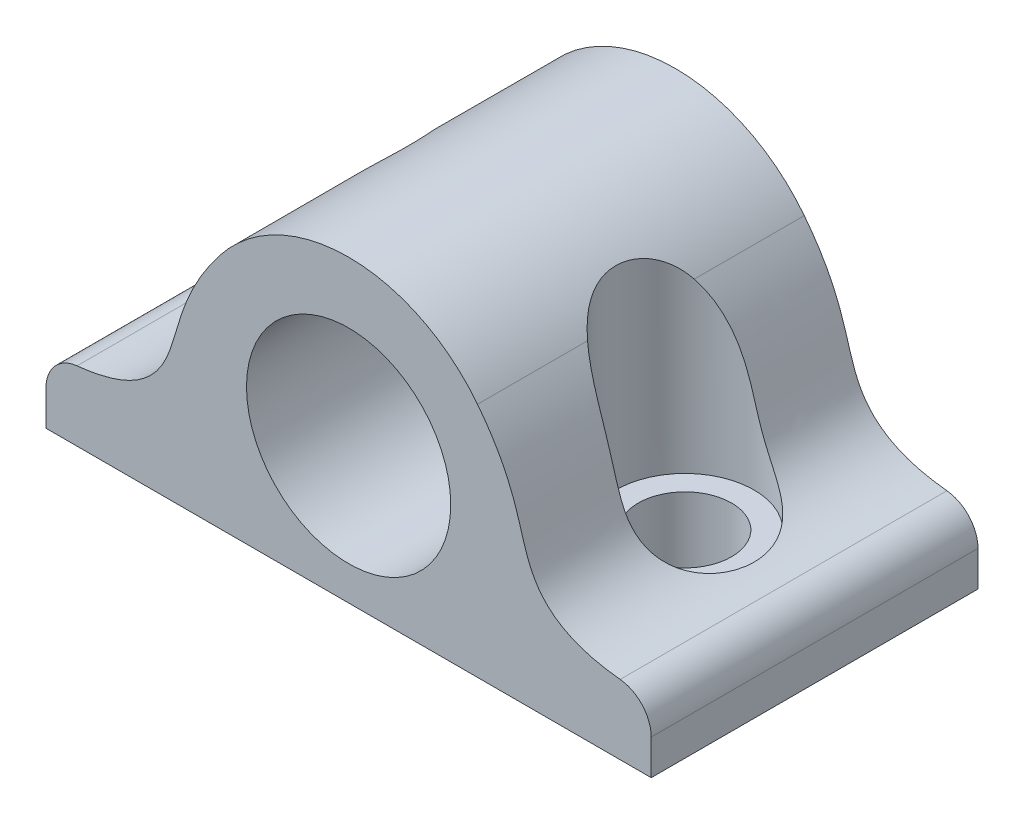
SolidWorks part; units mm, degrees
material "ABS"
ref_plane "Front Plane" through (0, 0, 0) normal (0, 0, 1) x (1, 0, 0)
ref_plane "Top Plane" through (0, 0, 0) normal (0, 1, 0) x (1, 0, 0)
ref_plane "Right Plane" through (0, 0, 0) normal (1, 0, 0) x (0, 0, -1)
sketch "Sketch1" plane through (0, 0, 0) normal (0, 0, 1) x (1, 0, 0)
  line L0 (-22.225, -5) -> (22.225, -5) construction
  line L1 (22.225, -10) -> (-22.225, -10)
  line L2 (22.225, -10) -> (22.225, -5)
  line L4 (-22.225, -10) -> (-22.225, -5)
  line L5 (0, 12) -> (0, -10) construction
  line L7 (-7.7296, 9.6049) -> (-11.2054, 5.1418) construction
  circle A0 centre (0, 0) radius 7.5
  arc A1 (9.4675, 7.3734) -> (-9.4675, 7.3734) centre (0, 0) ccw
  spline S0 degree 3 poles (-22.225, -5) (-16.6311, -4.982) (-12.3227, -1.7284) (-12.5305, 3.4404) (-9.4675, 7.3734) knots 0 0 0 0 0.501955 1 1 1 1
  spline S1 degree 3 poles (22.225, -5) (16.6311, -4.982) (12.3227, -1.7284) (12.5305, 3.4404) (9.4675, 7.3734) knots 0 0 0 0 0.501955 1 1 1 1
  dimension "D1" = 15
  dimension "D5" = 24
  dimension "D2" = 10
  dimension "D3" = 44.45
  dimension "D4" = 5
  dimension "D6" = 8.7669
extrude "Boss-Extrude1" add sketch "Sketch1" along normal mid plane 24
sketch "Sketch3" plane through (0, -10, 0) normal (0, -1, 0) x (1, 0, 0)
  line L0 (12.7, 0) -> (-12.7, 0) construction
  circle A0 centre (-12.7, 0) radius 3.425
  circle A1 centre (12.7, 0) radius 3.425
  point P3 (0, 0)
  dimension "D2" = 6.85
  dimension "D3" = 6.85
  dimension "D1" = 25.4
extrude "Cut-Extrude1" cut sketch "Sketch3" against normal through all
fillet "Fillet1" radius 2.54 2 edges at (22.225, -5, 0) (-22.225, -5, 0)
ref_plane "Plane1" through (0, -5, 0) normal (0, -1, 0) x (-1, 0, 0)
sketch "Sketch4" plane through (0, -5, 0) normal (0, -1, 0) x (-1, 0, 0)
  circle A0 centre (12.7, 0) radius 5.08
  circle A1 centre (-12.7, 0) radius 5.08
  dimension "D1" = 10.16
  dimension "D2" = 10.16
extrude "Cut-Extrude2" cut sketch "Sketch4" against normal through all
